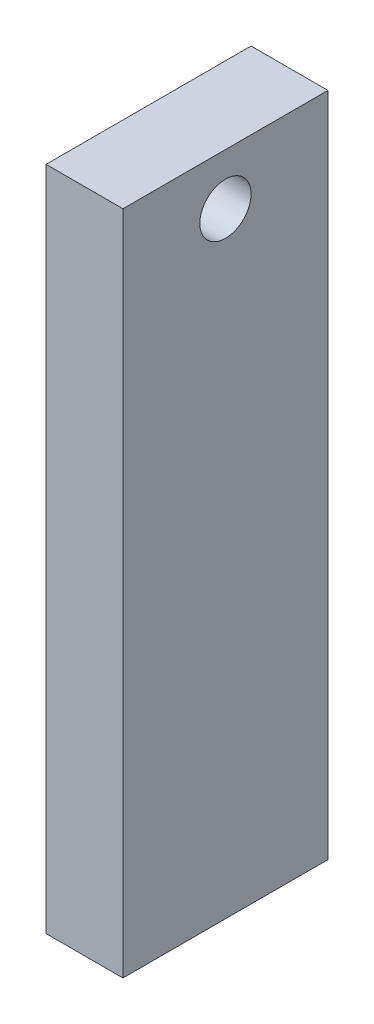
SolidWorks part; units mm, degrees
ref_plane "Front Plane" through (0, 0, 0) normal (0, 0, 1) x (1, 0, 0)
ref_plane "Top Plane" through (0, 0, 0) normal (0, 1, 0) x (1, 0, 0)
ref_plane "Right Plane" through (0, 0, 0) normal (1, 0, 0) x (0, 0, -1)
sketch "Sketch1" plane through (0, 0, 0) normal (1, 0, 0) x (0, 0, -1)
  line L1 (0, 0) -> (50.8, 0)
  line L2 (0, 0) -> (0, 165.1)
  line L3 (0, 165.1) -> (50.8, 165.1)
  line L4 (50.8, 0) -> (50.8, 165.1)
  circle A0 centre (25.4, 152.4) radius 6.35
  dimension "D3" = 12.7
  dimension "D1" = 165.1
  dimension "D2" = 50.8
  dimension "D4" = 12.7
  dimension "D5" = 25.4
extrude "Boss-Extrude1" add sketch "Sketch1" along normal blind 19.05
